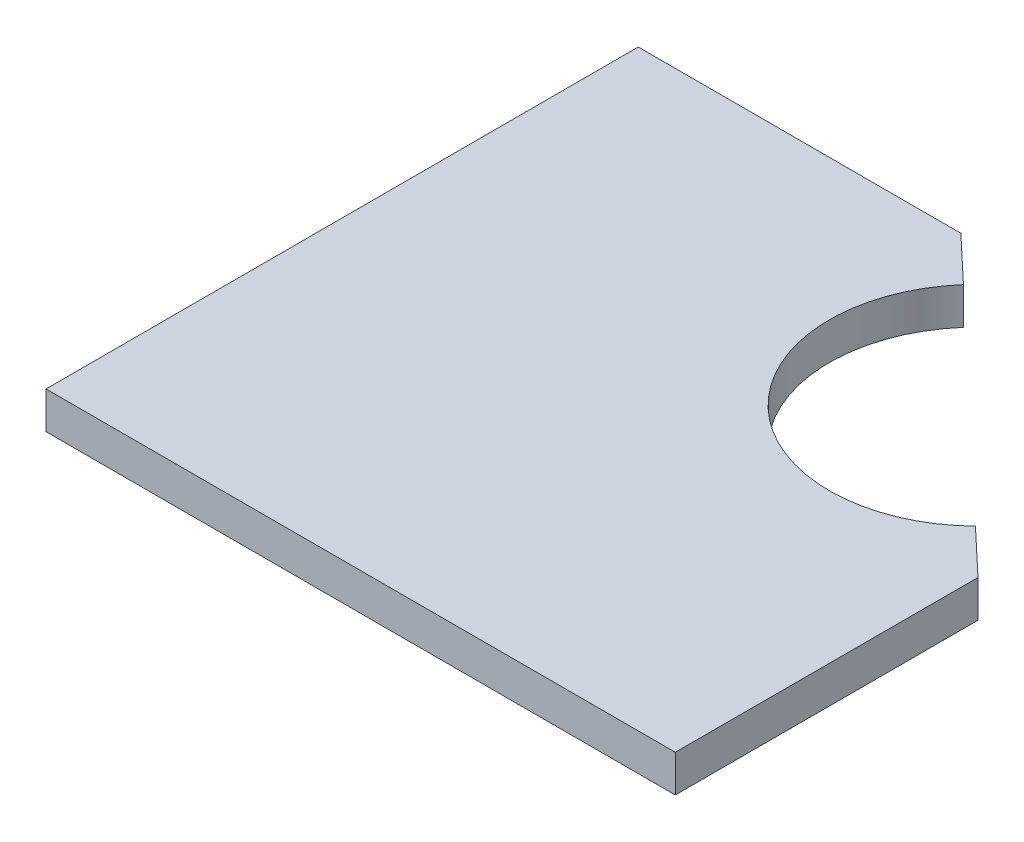
SolidWorks part; units mm, degrees
ref_plane "Face" through (0, 0, 0) normal (0, 0, 1) x (1, 0, 0)
ref_plane "Dessus" through (0, 0, 0) normal (0, 1, 0) x (1, 0, 0)
ref_plane "Droite" through (0, 0, 0) normal (1, 0, 0) x (0, 0, -1)
sketch "Esquisse1" plane through (0, 0, 0) normal (0, 1, 0) x (1, 0, 0)
  line L0 (-42.5, 40) -> (1.0757, 40)
  line L1 (42.5, -40) -> (-42.5, -40)
  line L2 (42.5, -40) -> (42.5, 40) construction
  line L3 (42.5, 40) -> (-42.5, 40) construction
  line L4 (-42.5, -40) -> (-42.5, 40)
  line L5 (42.5, -40) -> (-42.5, 40) construction
  line L6 (42.5, 40) -> (-42.5, -40) construction
  line L8 (42.5, 0.8886) -> (42.5, -40)
  line L10 (1.0757, 40) -> (7.2562, 34.1646)
  line L11 (36.3195, 6.724) -> (42.5, 0.8886)
  arc A0 (7.2562, 34.1646) -> (36.3195, 6.724) centre (22.3125, 21) ccw
  point P0 (0, 0)
  dimension "D1" = 80
  dimension "D3" = 40
  dimension "D4" = 61
  dimension "D5" = 64.8125
  dimension "D2" = 85
  dimension "D6" = 8.5
extrude "Boss.-Extru.1" add sketch "Esquisse1" along normal blind 5
sketch "Esquisse2" plane through (0, 0, 0) normal (0, -1, 0) x (1, 0, 0)
  arc A0 (36.3195, -6.724) -> (7.2562, -34.1646) centre (22.3125, -21) ccw construction
  point P1 (8.5822, -6.4577)
